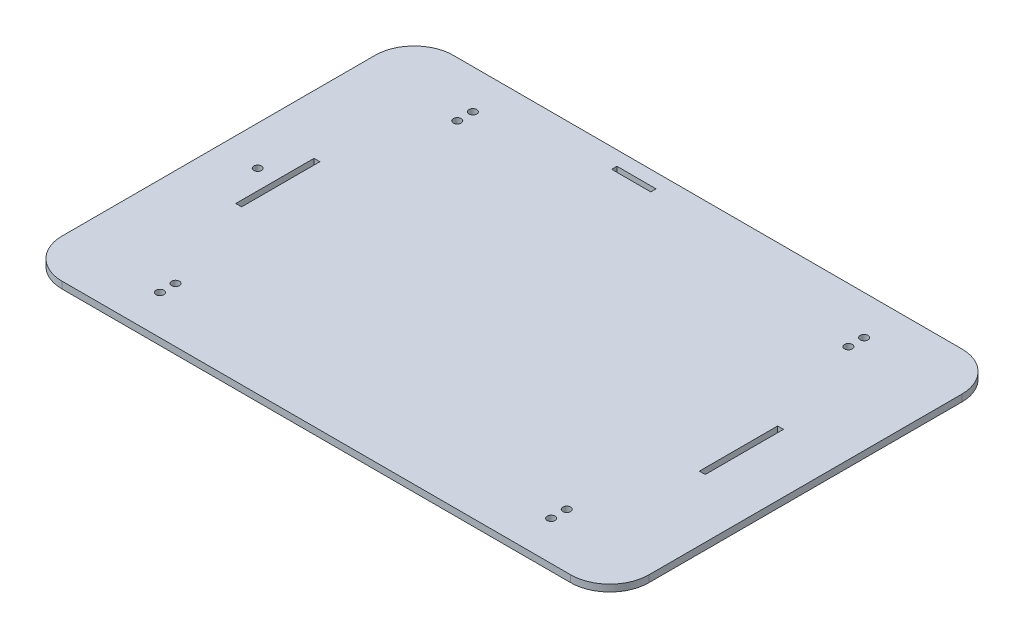
SolidWorks part; units mm, degrees
material "Acrylic (Medium-high impact)"
ref_plane "Front Plane" through (0, 0, 0) normal (0, 0, 1) x (1, 0, 0)
ref_plane "Top Plane" through (0, 0, 0) normal (0, 1, 0) x (1, 0, 0)
ref_plane "Right Plane" through (0, 0, 0) normal (1, 0, 0) x (0, 0, -1)
sketch "Sketch1" plane through (0, 0, 0) normal (0, 1, 0) x (1, 0, 0)
  line L1 (130, -100) -> (-130, -100)
  line L2 (150, -80) -> (150, 80)
  line L3 (130, 100) -> (-130, 100)
  line L4 (-150, -80) -> (-150, 80)
  line L5 (100, -80) -> (-100, -80) construction
  line L6 (100, -80) -> (100, 80) construction
  line L7 (100, 80) -> (-100, 80) construction
  line L8 (-100, -80) -> (-100, 80) construction
  line L9 (100, -80) -> (-100, 80) construction
  line L10 (100, 80) -> (-100, -80) construction
  circle A0 centre (-100, 80) radius 2
  circle A1 centre (100, 80) radius 2
  circle A2 centre (100, -80) radius 2
  circle A3 centre (-100, -80) radius 2
  arc A4 (150, 80) -> (130, 100) centre (130, 80) ccw
  arc A5 (130, -100) -> (150, -80) centre (130, -80) ccw
  arc A6 (-130, -100) -> (-150, -80) centre (-130, -80) cw
  arc A7 (-130, 100) -> (-150, 80) centre (-130, 80) ccw
  circle A8 centre (-130, 0) radius 2
  point P0 (0, 0)
  point P6 (-150, 0)
  point P7 (0, 0)
  point P18 (150, 100)
  point P23 (-150, -100)
  point P26 (-150, 100)
  dimension "D6" = 4
  dimension "D7" = 20
  dimension "D8" = 4
  dimension "D1" = 300
  dimension "D2" = 200
  dimension "D3" = 200
  dimension "D4" = 20
  dimension "D5" = 160
  dimension "D9" = 20
extrude "Boss-Extrude1" add sketch "Sketch1" along normal blind 3.5
sketch "Sketch3" plane through (0, 3.5, 0) normal (0, 1, 0) x (1, 0, 0)
  line L0 (-120, 18.7859) -> (-120, -21.2141)
  line L1 (-120, -21.2141) -> (-117, -21.2141)
  line L2 (-117, -21.2141) -> (-117, 18.7859)
  line L3 (-117, 18.7859) -> (-120, 18.7859)
  line L4 (0, 0) -> (0, 21.563) construction
  line L5 (120, -21.2141) -> (117, -21.2141)
  line L6 (117, 18.7859) -> (120, 18.7859)
  line L7 (120, 18.7859) -> (120, -21.2141)
  line L8 (117, -21.2141) -> (117, 18.7859)
  line L9 (-12.77, 0) -> (15.5692, 0) construction
  line L10 (-39.0502, 92.699) -> (-19.0502, 92.699)
  line L11 (-39.0502, 92.699) -> (-39.0502, 90)
  line L12 (-39.0502, 90) -> (-19.0502, 90)
  line L13 (-19.0502, 92.699) -> (-19.0502, 90)
  circle A0 centre (-100, 72) radius 2
  circle A1 centre (-100, 80) radius 2 construction
  circle A2 centre (-100, -72) radius 2
  circle A3 centre (100, -72) radius 2
  circle A4 centre (100, 72) radius 2
  dimension "D1" = 4
  dimension "D2" = 8
  dimension "D3" = 3
  dimension "D4" = 40
  dimension "D5" = 117
  dimension "D6" = 90
  dimension "D7" = 20
extrude "Cut-Extrude2" cut sketch "Sketch3" against normal blind 10
